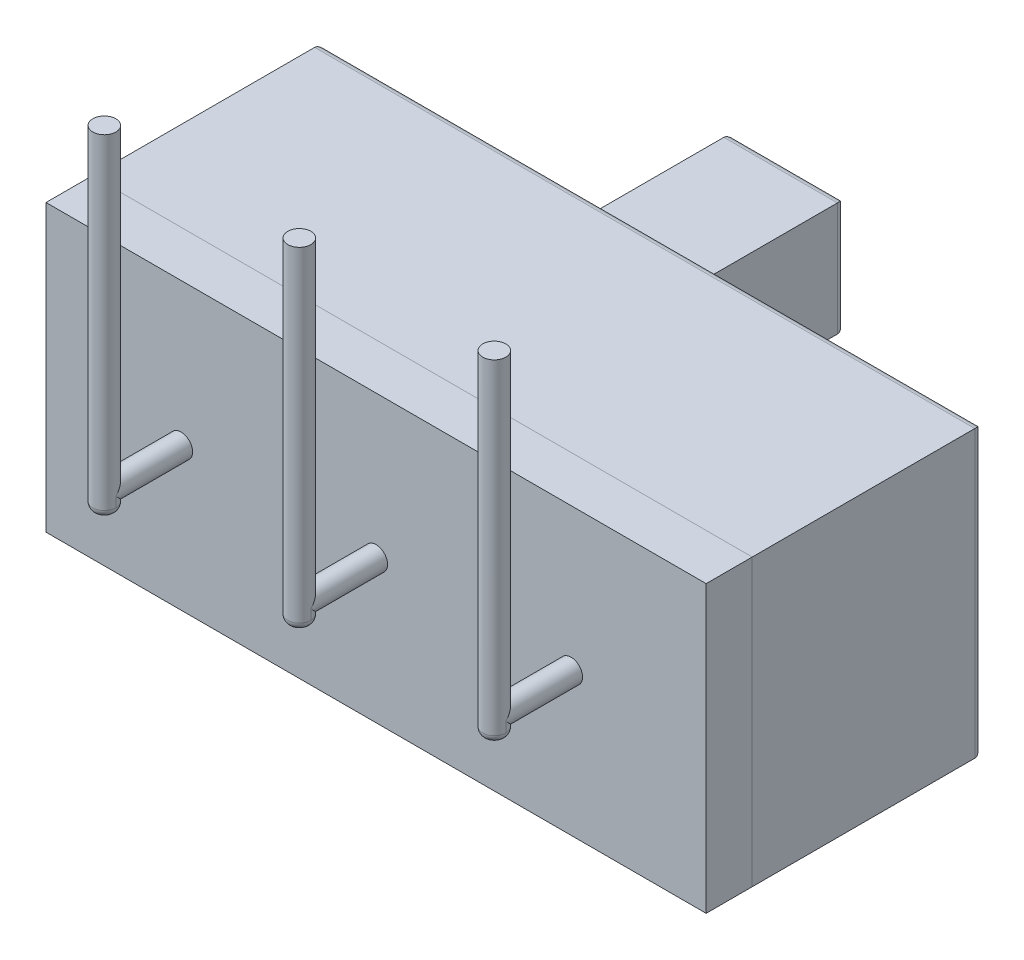
SolidWorks part; units mm, degrees
ref_plane "Спереди" through (0, 0, 0) normal (0, 0, 1) x (1, 0, 0)
ref_plane "Сверху" through (0, 0, 0) normal (0, 1, 0) x (1, 0, 0)
ref_plane "Справа" through (0, 0, 0) normal (1, 0, 0) x (0, 0, -1)
sketch "Эскиз1" plane through (0, 0, 0) normal (0, 0, 1) x (1, 0, 0)
  line L1 (-4.3, 1.86) -> (4.3, 1.86)
  line L2 (-4.3, 1.86) -> (-4.3, -1.86)
  line L3 (-4.3, -1.86) -> (4.3, -1.86)
  line L4 (4.3, 1.86) -> (4.3, -1.86)
  line L5 (-4.3, 1.86) -> (4.3, -1.86) construction
  line L6 (-4.3, -1.86) -> (4.3, 1.86) construction
  point P0 (0, 0)
  dimension "D1" = 8.6
  dimension "D2" = 3.72
extrude "Бобышка-Вытянуть1" add sketch "Эскиз1" along normal blind 3
sketch "Эскиз2" plane through (0, 0, 3) normal (0, 0, 1) x (1, 0, 0)
  line L1 (-4.3, 1.86) -> (4.3, 1.86)
  line L2 (-4.3, 1.86) -> (-4.3, -1.86)
  line L3 (-4.3, -1.86) -> (4.3, -1.86)
  line L4 (4.3, 1.86) -> (4.3, -1.86)
  line L5 (-4.3, 1.86) -> (4.3, -1.86) construction
  line L6 (-4.3, -1.86) -> (4.3, 1.86) construction
  point P0 (0, 0)
extrude "Бобышка-Вытянуть2" add sketch "Эскиз2" along normal blind 0.6 separate body
sketch "Эскиз3" plane through (0, 0, 0) normal (0, 0, -1) x (-1, 0, 0)
  line L1 (-1.75, 0.75) -> (1.75, 0.75)
  line L2 (-1.75, 0.75) -> (-1.75, -0.75)
  line L3 (-1.75, -0.75) -> (1.75, -0.75)
  line L4 (1.75, 0.75) -> (1.75, -0.75)
  line L5 (-1.75, 0.75) -> (1.75, -0.75) construction
  line L6 (-1.75, -0.75) -> (1.75, 0.75) construction
  point P0 (0, 0)
  dimension "D1" = 3.5
  dimension "D2" = 1.5
extrude "Вырез-Вытянуть1" cut sketch "Эскиз3" against normal blind 0.1 contours L1 L4 L3 L2
sketch "Эскиз4" plane through (0, 0, 0.1) normal (0, 0, -1) x (-1, 0, 0)
  line L0 (-1.75, 0.75) -> (1.75, 0.75) construction
  line L1 (0.26, 0.74) -> (1.74, 0.74)
  line L2 (0.26, 0.74) -> (0.26, -0.74)
  line L3 (0.26, -0.74) -> (1.74, -0.74)
  line L4 (1.74, 0.74) -> (1.74, -0.74)
  line L5 (0.26, 0.74) -> (1.74, -0.74) construction
  line L6 (0.26, -0.74) -> (1.74, 0.74) construction
  line L7 (1.75, 0.75) -> (1.75, -0.75) construction
  point P0 (1, 0)
  dimension "D1" = 0.01
  dimension "D2" = 1.48
  dimension "D3" = 0.01
  dimension "D4" = 1.48
extrude "Бобышка-Вытянуть3" add sketch "Эскиз4" along normal blind 2.87
fillet "Скругление1" radius 0.1 4 edges at (-1, -0.74, -2.77) (-1.74, 0, -2.77) (-1, 0.74, -2.77) (-0.26, 0, -2.77)
fillet "Скругление2" radius 0.1 4 edges at (-4.3, 0, 0) (0, -1.86, 0) (4.3, 0, 0) (0, 1.86, 0)
sketch "Эскиз5" plane through (0, 0, 3.6) normal (0, 0, 1) x (1, 0, 0)
  circle A0 centre (0, 0) radius 0.15
  circle A1 centre (-2.54, 0) radius 0.15
  circle A2 centre (2.54, 0) radius 0.15
  dimension "D3" = 0.3
  dimension "D4" = 0.3
  dimension "D5" = 0.3
  dimension "D1" = 2.54
  dimension "D2" = 2.54
extrude "Бобышка-Вытянуть4" add sketch "Эскиз5" along normal blind 1 separate body
ref_plane "Плоскость1" through (0, 0.01, 0) normal (0, -1, 0) x (-1, 0, 0)
sketch "Эскиз6" plane through (0, 0.01, 0) normal (0, -1, 0) x (-1, 0, 0)
  line L0 (-2.69, -4.6) -> (-2.39, -4.6) construction
  line L1 (-0.15, -4.6) -> (0.15, -4.6) construction
  line L2 (2.39, -4.6) -> (2.69, -4.6) construction
  circle A0 centre (-2.54, -4.6) radius 0.15
  circle A1 centre (0, -4.6) radius 0.15
  circle A2 centre (2.54, -4.6) radius 0.15
  dimension "D1" = 0.3
  dimension "D2" = 0.3
  dimension "D3" = 0.3
extrude "Бобышка-Вытянуть5" add sketch "Эскиз6" against normal blind 4.1 and the other way blind 0.24
fillet "Скругление3" radius 0.1 1 edges at (2.54, -0.23, 4.45)
fillet "Скругление4" radius 0.1 1 edges at (0, -0.23, 4.45)
fillet "Скругление5" radius 0.1 1 edges at (-2.54, -0.23, 4.45)
